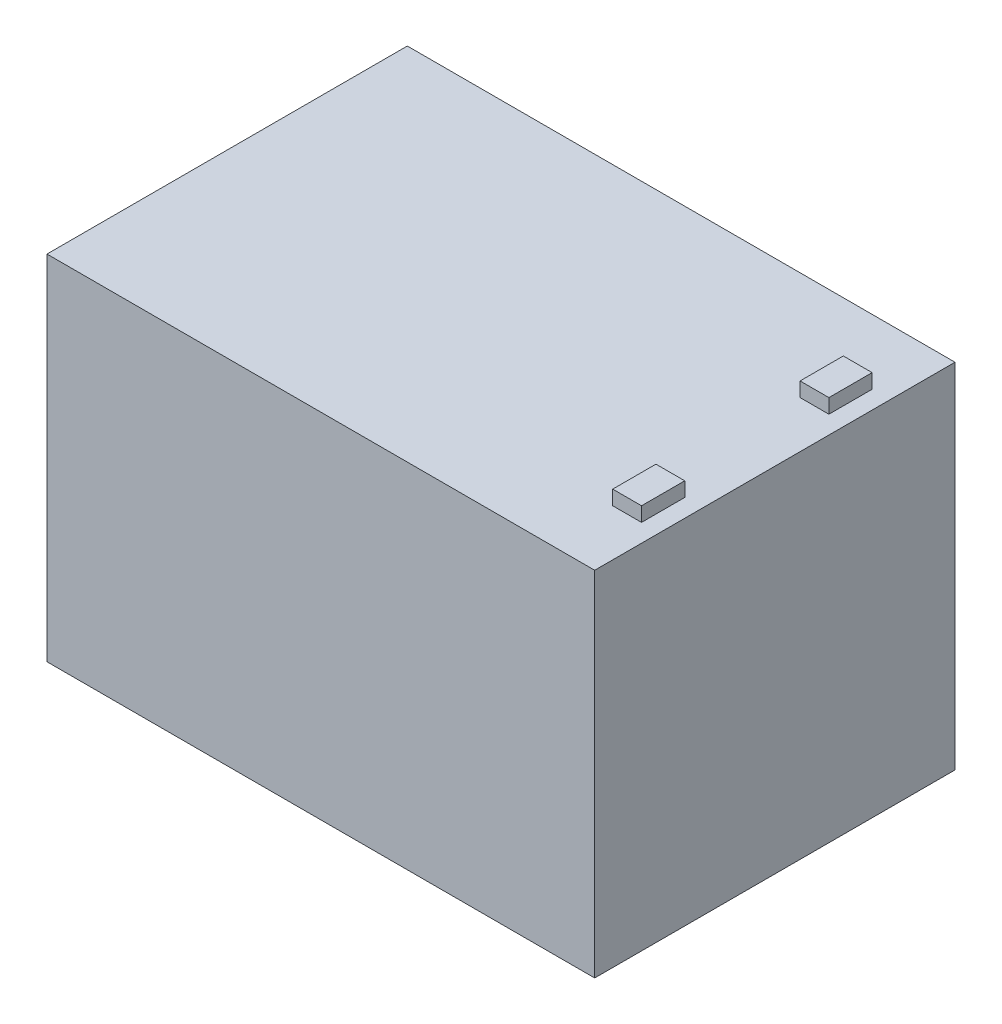
SolidWorks part; units mm, degrees
ref_plane "Спереди" through (0, 0, 0) normal (0, 0, 1) x (1, 0, 0)
ref_plane "Сверху" through (0, 0, 0) normal (0, 1, 0) x (1, 0, 0)
ref_plane "Справа" through (0, 0, 0) normal (1, 0, 0) x (0, 0, -1)
sketch "Sketch1" plane through (0, 0, 0) normal (0, 0, 1) x (1, 0, 0)
  line L1 (-76, -49) -> (76, -49)
  line L2 (-76, -49) -> (-76, 49)
  line L3 (-76, 49) -> (76, 49)
  line L4 (76, -49) -> (76, 49)
  line L5 (-76, -49) -> (76, 49) construction
  line L6 (-76, 49) -> (76, -49) construction
  point P0 (0, 0)
  dimension "D1" = 152
  dimension "D2" = 98
extrude "Boss-Extrude1" add sketch "Sketch1" along normal blind 100
sketch "Sketch2" plane through (0, 49, 0) normal (0, 1, 0) x (1, 0, 0)
  line L0 (76, 0) -> (-76, 0) construction
  line L1 (63, -18) -> (71, -18)
  line L2 (63, -18) -> (63, -30)
  line L3 (63, -30) -> (71, -30)
  line L4 (71, -18) -> (71, -30)
  line L5 (63, -18) -> (71, -30) construction
  line L6 (63, -30) -> (71, -18) construction
  line L7 (63, -70) -> (71, -70)
  line L8 (63, -70) -> (63, -82)
  line L9 (63, -82) -> (71, -82)
  line L10 (71, -70) -> (71, -82)
  line L11 (63, -70) -> (71, -82) construction
  line L12 (63, -82) -> (71, -70) construction
  line L13 (76, -100) -> (76, 0) construction
  line L14 (76, -100) -> (-76, -100) construction
  point P0 (67, -24)
  point P5 (67, -76)
  dimension "D1" = 18
  dimension "D2" = 5
  dimension "D3" = 12
  dimension "D4" = 8
  dimension "D5" = 18
  dimension "D6" = 5
  dimension "D7" = 8
  dimension "D8" = 12
extrude "Boss-Extrude2" add sketch "Sketch2" along normal blind 4
